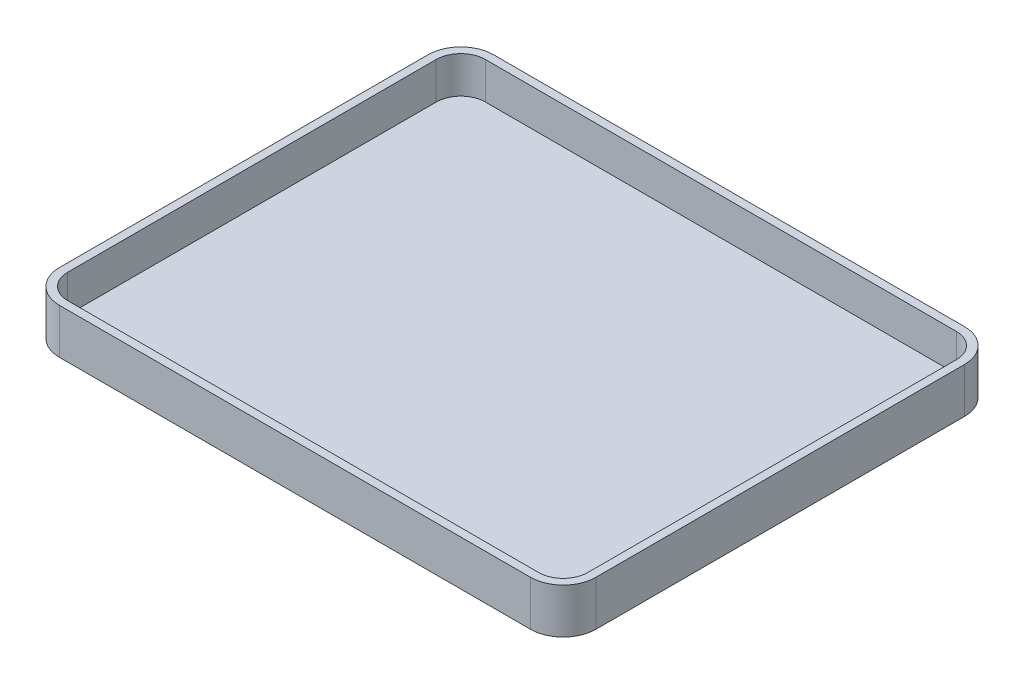
SolidWorks part; units mm, degrees
ref_plane "Alzado" through (0, 0, 0) normal (0, 0, 1) x (1, 0, 0)
ref_plane "Planta" through (0, 0, 0) normal (0, 1, 0) x (1, 0, 0)
ref_plane "Vista lateral" through (0, 0, 0) normal (1, 0, 0) x (0, 0, -1)
sketch "Croquis1" plane through (0, 0, 0) normal (0, 1, 0) x (1, 0, 0)
  line L0 (-65.5, 53) -> (-65.5, -53)
  line L1 (-63.5, 51) -> (63.5, 51)
  line L2 (-63.5, 51) -> (-63.5, -51)
  line L3 (-63.5, -51) -> (63.5, -51)
  line L4 (63.5, 51) -> (63.5, -51)
  line L5 (-63.5, 51) -> (63.5, -51) construction
  line L6 (-63.5, -51) -> (63.5, 51) construction
  line L7 (-65.5, -53) -> (65.5, -53)
  line L8 (65.5, 53) -> (65.5, -53)
  line L9 (-65.5, 53) -> (65.5, 53)
  line L10 (-60.3314, 19.4071) -> (299.002, 19.4071) construction
  line L11 (-45.0261, 11.6734) -> (-40.4305, 12.8223)
  line L12 (-39.5114, 12.8223) -> (-44.3368, 10.065)
  line L13 (-17.4526, 6.8481) -> (-13.5464, 6.6183)
  line L14 (-13.5464, 6.6183) -> (-10.5592, -1.8835)
  line L15 (-10.5592, -1.8835) -> (-7.5721, 6.6183)
  line L16 (-3.6659, 6.6183) -> (-3.8956, -6.0196)
  line L17 (-3.8956, -6.0196) -> (-5.9636, -5.7898)
  line L18 (-5.9636, -5.7898) -> (-6.1934, 2.9418)
  line L19 (-6.1934, 2.9418) -> (-9.6401, -6.0196)
  line L20 (-9.6401, -6.0196) -> (-11.7081, -5.7898)
  line L21 (-11.7081, -5.7898) -> (-14.925, 2.9418)
  line L22 (-14.925, 2.9418) -> (-15.3846, -6.0196)
  line L23 (-15.3846, -6.0196) -> (-17.4526, -5.7898)
  line L24 (-17.4526, -5.7898) -> (-17.4526, 6.8481)
  line L25 (7.5933, -2.1133) -> (1.1595, -2.3431)
  line L26 (5.5253, -3.2622) -> (7.5933, -3.492)
  line L27 (4.3764, 1.3334) -> (5.0658, -0.0453)
  line L28 (5.0658, -0.0453) -> (1.1595, -0.0453)
  line L29 (16.3249, 7.0778) -> (18.8525, 6.8481)
  line L30 (18.8525, 6.8481) -> (18.6227, -6.2493)
  line L31 (18.6227, -6.2493) -> (16.3249, -6.0196)
  line L32 (16.0952, 2.4823) -> (16.3249, 7.0778)
  line L33 (20.0014, 3.4014) -> (22.7588, 3.1716)
  line L34 (22.7588, 3.1716) -> (24.3672, -2.5729)
  line L35 (24.3672, -2.5729) -> (26.2054, 3.4014)
  line L36 (26.2054, 3.4014) -> (28.733, 3.1716)
  line L37 (28.733, 3.1716) -> (30.3415, -2.8027)
  line L38 (30.3415, -2.8027) -> (32.1797, 3.4014)
  line L39 (32.1797, 3.4014) -> (34.7073, 3.1716)
  line L40 (34.7073, 3.1716) -> (31.7201, -6.2493)
  line L41 (31.7201, -6.2493) -> (28.9628, -6.0196)
  line L42 (28.9628, -6.0196) -> (27.3543, -0.2751)
  line L43 (27.3543, -0.2751) -> (25.7459, -6.2493)
  line L44 (25.7459, -6.2493) -> (22.7588, -6.0196)
  line L45 (22.7588, -6.0196) -> (20.0014, 3.4014)
  line L46 (38.3837, 0.4142) -> (35.8562, 0.644)
  line L47 (41.6006, -1.6538) -> (41.8304, -2.8027)
  line L48 (38.6135, -4.4111) -> (38.154, -3.492)
  line L49 (45.5069, 3.4014) -> (48.494, 3.1716)
  line L50 (48.494, 3.1716) -> (50.3322, -2.8027)
  line L51 (50.3322, -2.8027) -> (52.4003, 3.4014)
  line L52 (52.4003, 3.4014) -> (55.1576, 3.1716)
  line L53 (46.1962, -9.4663) -> (46.426, -7.1685)
  line L54 (46.426, -7.1685) -> (47.8047, -7.3982)
  ellipse E0 centre (14.0074, -1.4088) end of major axis (14.1398, -4.5131) minor radius 2.2912
  spline S0 degree 3 poles (-44.3368, 10.065) (-44.4134, 9.8352) (-44.3953, 9.5469) (-44.5665, 9.3756) (-44.8087, 9.1334) (-45.2601, 9.1739) (-45.4857, 8.9161) (-45.824, 8.5294) (-45.8763, 7.9555) (-46.175, 7.5374) (-46.2745, 7.398) (-46.5276, 7.4414) (-46.6345, 7.3076) (-46.8485, 7.0401) (-46.9041, 6.6735) (-47.0941, 6.3885) (-47.2143, 6.2083) (-47.4568, 6.1227) (-47.5537, 5.9289) (-47.6949, 5.6465) (-47.6662, 5.303) (-47.7834, 5.0098) (-47.8237, 4.9093) (-47.9743, 4.8811) (-48.0132, 4.7801) (-48.361, 3.8758) (-48.7538, 2.9749) (-48.9323, 2.0227) (-49.2161, 0.5096) (-49.2387, -1.041) (-49.3919, -2.5729) knots 0 0 0 0 1 1 1 2 2 2 3 3 3 4 4 4 5 5 5 6 6 6 7 7 7 8 8 8 9 9 9 10 10 10 10
  spline S1 degree 3 poles (-49.3919, -3.0324) (-50.4276, -2.5146) (-50.8616, -2.0701) (-51.2301, -0.9644) knots 0 0 0 0 1 1 1 1
  spline S2 degree 3 poles (-51.9195, -0.7346) (-52.0727, 0.1845) (-52.4564, 1.0941) (-52.379, 2.0227) (-52.2337, 3.7666) (-51.3282, 5.4241) (-50.311, 6.8481) (-49.9962, 7.2888) (-49.4946, 7.5694) (-49.1621, 7.997) (-48.9518, 8.2673) (-48.9448, 8.6739) (-48.7026, 8.9161) (-48.5313, 9.0873) (-48.2103, 9.0051) (-48.0132, 9.1459) (-47.8677, 9.2498) (-46.7756, 10.5954) (-46.4048, 10.7543) (-46.0458, 10.9082) (-45.6388, 10.9075) (-45.2559, 10.9841) knots 0 0 0 0 1 1 1 2 2 2 3 3 3 4 4 4 5 5 5 6 6 6 7 7 7 7
  spline S3 degree 3 poles (-31.0096, -6.7089) (-31.3306, -7.1583) (-31.5555, -7.6804) (-31.9287, -8.0876) (-32.6643, -8.89) (-33.5505, -9.5518) (-34.4563, -10.1556) (-35.0575, -10.5564) (-35.6407, -10.9968) (-36.2945, -11.3045) (-36.952, -11.6139) (-37.6638, -11.7942) (-38.3625, -11.9938) (-39.2735, -12.2541) (-40.1743, -12.6241) (-41.1198, -12.6832) (-43.7095, -12.845) (-44.9482, -12.7603) (-46.8643, -11.9938) (-46.9649, -11.9536) (-46.9935, -11.8043) (-47.0941, -11.764) (-47.3873, -11.6468) (-47.72, -11.6516) (-48.0132, -11.5343) (-48.2144, -11.4538) (-48.3196, -11.2279) (-48.4728, -11.0747) (-49.123, -10.4245) (-49.8231, -9.7996) (-50.311, -9.0067) (-50.6701, -8.4233) (-50.9805, -7.8064) (-51.2301, -7.1685) (-52.4275, -4.1086) (-52.379, -4.8655) (-52.379, -3.2622) knots 13 13 13 13 14 14 14 15 15 15 16 16 16 17 17 17 18 18 18 19 19 19 20 20 20 21 21 21 22 22 22 23 23 23 24 24 24 25 25 25 25
  spline S4 degree 3 poles (-52.379, -3.2622) (-52.0727, -3.3388) (-51.7102, -3.2995) (-51.4599, -3.492) (-50.6872, -4.0864) (-50.1361, -4.9303) (-49.3919, -5.56) (-49.1304, -5.7813) (-48.7515, -5.8205) (-48.4728, -6.0196) (-48.2084, -6.2084) (-48.0741, -6.5636) (-47.7834, -6.7089) (-47.2847, -6.9583) (-46.6971, -6.9727) (-46.175, -7.1685) (-46.0736, -7.2065) (-46.0458, -7.358) (-45.9452, -7.3982) (-45.2706, -7.6681) (-44.5897, -7.9451) (-43.8772, -8.0876) (-42.6662, -8.3298) (-41.435, -8.5046) (-40.2007, -8.5471) (-38.2981, -8.6127) (-35.8994, -8.005) (-34.2265, -7.1685) (-33.7047, -6.9076) (-33.1398, -6.74) (-32.618, -6.4791) (-31.9717, -6.156) (-31.4653, -5.5587) (-30.7798, -5.3302) (-30.6173, -5.2761) (-30.3202, -5.3887) (-30.3202, -5.56) (-30.3202, -6.4618) (-30.6982, -6.273) (-31.0096, -6.7089) knots 0 0 0 0 1 1 1 2 2 2 3 3 3 4 4 4 5 5 5 6 6 6 7 7 7 8 8 8 9 9 9 10 10 10 11 11 11 12 12 12 13 13 13 13
  spline S5 degree 3 poles (-31.4691, -14.0618) (-34.1314, -15.2906) (-37.3071, -15.9228) (-40.2007, -15.4405) (-40.3076, -15.4227) (-40.3239, -15.2301) (-40.4305, -15.2107) (-41.1878, -15.073) (-41.9981, -15.2244) (-42.7283, -14.981) (-42.8908, -14.9268) (-42.6559, -14.5889) (-42.4985, -14.5214) (-42.0703, -14.3379) (-41.58, -14.3643) (-41.1198, -14.2916) (-40.1248, -14.1345) (-39.1178, -14.0431) (-38.1327, -13.8321) (-38.0268, -13.8094) (-38.0035, -13.6425) (-37.9029, -13.6023) (-37.2283, -13.3324) (-36.5096, -13.1828) (-35.8349, -12.9129) (-35.2275, -12.67) (-34.5809, -12.1146) (-33.9967, -11.764) (-32.5277, -10.8827) (-31.8287, -10.3179) (-30.7798, -9.0067) (-30.5091, -8.6684) (-30.0836, -8.4591) (-29.8607, -8.0876) (-29.5606, -7.5874) (-29.4322, -7.0009) (-29.1713, -6.4791) (-28.4572, -5.0508) (-27.8289, -3.9389) (-27.5629, -2.3431) (-27.4097, -1.424) (-27.1033, -0.5175) (-27.1033, 0.4142) (-27.1033, 2.7445) (-27.4377, 4.2444) (-28.0224, 6.3885) (-28.0509, 6.493) (-28.2038, 6.5214) (-28.2522, 6.6183) (-28.6661, 7.4461) (-28.9623, 8.331) (-29.4011, 9.1459) (-29.5038, 9.3366) (-29.7405, 9.4252) (-29.8607, 9.6054) (-30.0507, 9.8904) (-30.2531, 10.1886) (-30.3202, 10.5245) (-30.3415, 10.6307) (-30.167, 10.6777) (-30.0905, 10.7543) knots 20 20 20 20 21 21 21 22 22 22 23 23 23 24 24 24 25 25 25 26 26 26 27 27 27 28 28 28 29 29 29 30 30 30 31 31 31 32 32 32 33 33 33 34 34 34 35 35 35 36 36 36 37 37 37 38 38 38 39 39 39 40 40 40 40
  spline S6 degree 3 poles (-30.0905, 10.7543) (-29.1914, 10.4546) (-28.9328, 10.1923) (-28.2522, 9.3756) (-28.1426, 9.2441) (-28.1595, 9.0188) (-28.0224, 8.9161) (-27.8287, 8.7707) (-27.5044, 8.8576) (-27.3331, 8.6863) (-26.4894, 7.8426) (-26.1071, 6.6787) (-25.4949, 5.6992) (-25.3801, 5.5155) (-25.1158, 5.4408) (-25.0353, 5.2396) (-24.8007, 4.6532) (-24.7755, 4.0006) (-24.5758, 3.4014) (-24.5415, 3.2986) (-24.3722, 3.2767) (-24.346, 3.1716) (-24.0618, 2.0349) (-23.6892, 0.8961) (-23.6566, -0.2751) (-23.6118, -1.8902) (-23.8979, -3.4995) (-24.1162, -5.1005) (-24.1308, -5.2078) (-24.3117, -5.2275) (-24.346, -5.3302) (-24.5457, -5.9294) (-24.571, -6.582) (-24.8055, -7.1685) (-24.886, -7.3696) (-25.1536, -7.4423) (-25.2651, -7.628) (-25.4413, -7.9217) (-25.5282, -8.2665) (-25.7246, -8.5471) (-26.1997, -9.2259) (-26.5787, -9.9739) (-27.1033, -10.6152) (-27.2782, -10.8289) (-27.6201, -10.8591) (-27.7927, -11.0747) (-27.944, -11.2638) (-27.8512, -11.5928) (-28.0224, -11.764) (-28.2646, -12.0063) (-28.6628, -12.0245) (-28.9416, -12.2236) (-29.206, -12.4125) (-29.3665, -12.7241) (-29.6309, -12.9129) (-29.9096, -13.112) (-30.2595, -13.191) (-30.55, -13.3725) (-30.8748, -13.5755) (-31.1214, -13.9014) (-31.4691, -14.0618) knots 0 0 0 0 1 1 1 2 2 2 3 3 3 4 4 4 5 5 5 6 6 6 7 7 7 8 8 8 9 9 9 10 10 10 11 11 11 12 12 12 13 13 13 14 14 14 15 15 15 16 16 16 17 17 17 18 18 18 19 19 19 20 20 20 20
  spline S7 degree 3 poles (-7.5721, 6.6183) (-7.1125, 6.6949) (-6.6593, 6.8481) (-6.1934, 6.8481) (-5.3474, 6.8481) (-4.5084, 6.6949) (-3.6659, 6.6183) knots 0 0 0 0 1 1 1 2 2 2 2
  spline S8 degree 3 poles (7.5933, -3.492) (7.3373, -4.5162) (7.5869, -4.1878) (7.1338, -4.6409) (6.7508, -5.0239) (6.4551, -5.5211) (5.9849, -5.7898) (5.354, -6.1503) (4.6402, -6.4102) (3.9169, -6.4791) (2.772, -6.5882) (1.0085, -6.4331) (0.0106, -5.56) (-1.7342, -4.0333) (-1.7519, -1.9723) (-1.5978, 0.1845) (-1.5901, 0.2925) (-1.4165, 0.3174) (-1.3681, 0.4142) (-1.1072, 0.936) (-1.0218, 1.551) (-0.6787, 2.0227) (-0.3903, 2.4193) (0.0564, 2.6785) (0.4702, 2.9418) (0.9036, 3.2177) (1.3374, 3.5824) (1.8488, 3.6312) (2.9951, 3.7403) (4.153, 3.5442) (5.2955, 3.4014) (5.403, 3.3879) (5.4407, 3.2393) (5.5253, 3.1716) (6.1856, 2.6433) (7.0143, 2.1715) (7.3635, 1.3334) (7.6065, 0.7503) (7.7811, 0.1253) (7.8231, -0.5049) (7.8591, -1.0453) (7.6699, -1.5772) (7.5933, -2.1133) knots 0 0 0 0 1 1 1 2 2 2 3 3 3 4 4 4 5 5 5 6 6 6 7 7 7 8 8 8 9 9 9 10 10 10 11 11 11 12 12 12 13 13 13 14 14 14 14
  spline S9 degree 3 poles (1.1595, -2.3431) (1.2459, -2.7752) (1.2618, -3.7) (1.8488, -3.9516) (3.6525, -4.7246) (4.1926, -4.595) (5.5253, -3.2622) knots 0 0 0 0 1 1 1 2 2 2 2
  spline S10 degree 3 poles (1.1595, -0.0453) (1.3494, 0.4294) (1.5251, 1.4979) (2.3084, 1.5631) (2.9996, 1.6207) (3.6871, 1.41) (4.3764, 1.3334) knots 0 0 0 0 1 1 1 2 2 2 2
  spline S11 degree 3 poles (16.0952, -5.3302) (15.3292, -6.0962) (14.4647, -6.4791) (13.3378, -6.4791) (12.7203, -6.4791) (12.1024, -6.3833) (11.4996, -6.2493) (11.3938, -6.2259) (11.3464, -6.0962) (11.2698, -6.0196) (10.503, -5.2527) (9.7316, -4.7721) (9.4316, -3.7218) (8.9637, -2.0844) (8.6633, -0.6627) (9.4316, 0.8738) (9.616, 1.2427) (9.6335, 1.7006) (9.8911, 2.0227) (10.4795, 2.7581) (11.6436, 3.5684) (12.6485, 3.6312) (14.8723, 3.7701) (14.7322, 3.5045) (16.0952, 2.4823) knots 0 0 0 0 1 1 1 2 2 2 3 3 3 4 4 4 5 5 5 6 6 6 7 7 7 8 8 8 8
  spline S12 degree 3 poles (35.8562, 0.644) (36.0152, 1.5981) (35.9443, 2.1927) (36.7753, 2.712) (37.211, 2.9844) (37.7078, 3.1465) (38.154, 3.4014) (38.248, 3.4551) (38.2754, 3.6312) (38.3837, 3.6312) (42.8523, 3.6312) (41.9114, 4.4693) (43.2091, 3.1716) (43.5921, 2.7886) (44.2668, 2.5566) (44.358, 2.0227) (44.8228, -0.6995) (44.6644, -3.492) (44.8175, -6.2493) knots 0 0 0 0 1 1 1 2 2 2 3 3 3 4 4 4 5 5 5 6 6 6 6
  spline S13 degree 3 poles (44.8175, -6.2493) (41.8443, -6.0016) (42.7124, -6.6717) (41.6006, -5.56) knots 0 0 0 0 1 1 1 1
  spline S14 degree 3 poles (41.6006, -5.56) (41.4475, -5.7132) (41.3422, -5.9391) (41.1411, -6.0196) (40.5547, -6.2541) (39.9336, -6.4459) (39.3028, -6.4791) (38.4301, -6.5251) (36.3607, -6.5916) (35.8562, -5.3302) (35.354, -4.0748) (34.9988, -2.3019) (36.3157, -1.424) (36.6007, -1.234) (36.9025, -1.0475) (37.2348, -0.9644) (38.6776, -0.6037) (40.1707, -0.4539) (41.6006, -0.0453) knots 0 0 0 0 1 1 1 2 2 2 3 3 3 4 4 4 5 5 5 6 6 6 6
  spline S15 degree 3 poles (41.8304, 0.8738) (41.6006, 1.1036) (41.4453, 1.449) (41.1411, 1.5631) (39.5526, 2.1588) (39.0423, 1.7313) (38.3837, 0.4142) knots 0 0 0 0 1 1 1 2 2 2 2
  spline S16 degree 3 poles (41.8304, -2.8027) (41.5388, -3.0943) (41.6625, -3.6599) (41.3709, -3.9516) (40.3449, -4.9775) (39.8013, -4.6091) (38.6135, -4.4111) knots 0 0 0 0 1 1 1 2 2 2 2
  spline S17 degree 3 poles (38.154, -3.492) (38.3071, -3.1856) (38.3395, -2.7784) (38.6135, -2.5729) (39.4469, -1.9478) (40.5989, -1.94) (41.6006, -1.6538) knots 0 0 0 0 1 1 1 2 2 2 2
  spline S18 degree 3 poles (55.1576, 3.1716) (54.834, 1.8773) (54.475, 0.7385) (54.0087, -0.5049) (53.9707, -0.6063) (53.817, -0.6332) (53.7789, -0.7346) (53.5831, -1.2568) (53.5152, -1.821) (53.3194, -2.3431) (53.2813, -2.4445) (53.1276, -2.4715) (53.0896, -2.5729) (52.5965, -3.8879) (52.4338, -4.7046) (51.9407, -6.0196) (51.9027, -6.121) (51.749, -6.1479) (51.7109, -6.2493) (50.9769, -8.2066) (51.6932, -7.416) (51.0216, -8.0876) (50.6386, -8.4705) (50.3495, -8.9797) (49.8727, -9.2365) (48.4951, -9.9783) (47.6251, -9.6449) (46.1962, -9.4663) knots 0 0 0 0 1 1 1 2 2 2 3 3 3 4 4 4 5 5 5 6 6 6 7 7 7 8 8 8 9 9 9 9
  spline S19 degree 3 poles (48.494, -6.9387) (48.5706, -6.4791) (48.8198, -6.0159) (48.7238, -5.56) (48.504, -4.5161) (47.9532, -3.5704) (47.5749, -2.5729) (47.1107, -1.3491) (46.6395, -0.1279) (46.1962, 1.1036) (45.4827, 3.0857) (45.5069, 2.4617) (45.5069, 3.4014) knots 0 0 0 0 1 1 1 2 2 2 3 3 3 4 4 4 4
  point P0 (0, 0)
  dimension "D1" = 127
  dimension "D2" = 102
  dimension "D3" = 2
extrude "Saliente-Extruir2" add sketch "Croquis1" along normal blind 11
fillet "Redondeo1" radius 8 4 edges at (-65.5, 5.5, -53) (65.5, 5.5, -53) (65.5, 5.5, 53) (-65.5, 5.5, 53)
shell "Vaciado1" thickness 2
sketch "Croquis3" plane through (0, 0, 0) normal (0, -1, 0) x (1, 0, 0)
  line L0 (35.7047, 72.3651) -> (395.038, 72.3651) construction
  line L1 (-43.7957, -0.602) -> (-44.7734, -0.211)
  line L2 (-44.7734, -0.211) -> (-45.6758, 0.9833)
  line L3 (-16.3093, 8.1491) -> (-12.7264, 7.95)
  line L4 (-12.7264, 7.95) -> (-10.1388, 0.7843)
  line L5 (-10.1388, 0.7843) -> (-7.5512, 8.1491)
  line L6 (-7.5512, 8.1491) -> (-3.9683, 7.95)
  line L7 (-3.9683, 7.95) -> (-4.1673, -3.3958)
  line L8 (-4.1673, -3.3958) -> (-6.3569, -3.1967)
  line L9 (-6.3569, -3.1967) -> (-6.5559, 4.1681)
  line L10 (-6.5559, 4.1681) -> (-9.1436, -3.3958)
  line L11 (-9.1436, -3.3958) -> (-11.3331, -3.1967)
  line L12 (-11.3331, -3.1967) -> (-13.9207, 4.3672)
  line L13 (-13.9207, 4.3672) -> (-14.1198, -3.3958)
  line L14 (-14.1198, -3.3958) -> (-16.5084, -3.1967)
  line L15 (-16.5084, -3.1967) -> (-16.3093, 8.1491)
  line L16 (5.9842, 0.3862) -> (0.0127, -0.0119)
  line L17 (3.7946, -0.8081) -> (5.5861, -1.0072)
  line L18 (2.7994, 3.1729) -> (3.3965, 1.9786)
  line L19 (3.3965, 1.9786) -> (0.0127, 1.9786)
  line L20 (12.9509, 8.1491) -> (15.3395, 7.95)
  line L21 (15.3395, 7.95) -> (15.1404, -3.3958)
  line L22 (15.1404, -3.3958) -> (13.15, -3.1967)
  line L23 (12.9509, 4.1681) -> (12.9509, 8.1491)
  line L24 (16.3347, 4.9643) -> (18.7233, 4.7653)
  line L25 (18.7233, 4.7653) -> (20.1167, -0.211)
  line L26 (20.1167, -0.211) -> (21.51, 4.9643)
  line L27 (21.51, 4.9643) -> (23.8986, 4.7653)
  line L28 (23.8986, 4.7653) -> (25.292, -0.211)
  line L29 (25.292, -0.211) -> (26.6853, 4.9643)
  line L30 (26.6853, 4.9643) -> (29.0739, 4.7653)
  line L31 (29.0739, 4.7653) -> (26.4862, -3.3958)
  line L32 (26.4862, -3.3958) -> (23.8986, -3.1967)
  line L33 (23.8986, -3.1967) -> (22.7043, 1.5805)
  line L34 (22.7043, 1.5805) -> (21.311, -3.3958)
  line L35 (21.311, -3.3958) -> (18.7233, -3.1967)
  line L36 (18.7233, -3.1967) -> (16.3347, 4.9643)
  line L37 (32.0596, 2.3767) -> (30.0894, 2.3767)
  line L38 (35.4435, 0.5213) -> (35.2363, -1.0692)
  line L39 (38.4292, 4.9643) -> (41.0168, 4.7653)
  line L40 (41.0168, 4.7653) -> (42.6092, -0.41)
  line L41 (42.6092, -0.41) -> (44.4007, 4.9643)
  line L42 (44.4007, 4.9643) -> (46.7893, 4.7653)
  line L43 (39.0263, -5.9834) -> (39.2254, -4.192)
  line L44 (39.2254, -4.192) -> (40.6187, -4.391)
  line L45 (41.2159, -3.7939) -> (38.4292, 4.9643)
  line L49 (32.3732, 2.62) -> (32.2587, 2.3767)
  arc A0 (3.7946, -0.8081) -> (0.0127, -0.0119) centre (2.0311, 0.1953) cw
  ellipse E0 centre (11.1194, 0.8206) end of major axis (11.1554, -1.8699) minor radius 1.9649
  spline S0 degree 3 poles (-29.8447, -3.9929) (-29.2525, -3.7776) (-27.257, -1.7538) (-27.257, -2.5996) (-27.257, -4.1524) (-29.907, -6.3419) (-31.039, -6.9786) (-35.2673, -9.3571) (-42.0186, -10.4827) (-44.7734, -5.5853) (-45.5687, -4.1713) (-46.3658, -2.2563) (-46.3658, -0.6091) knots 4 4 4 4 5 5 5 6 6 6 7 7 7 8 8 8 8
  spline S1 degree 3 poles (-46.3658, -0.6091) (-46.1667, -0.6754) (-45.9325, -0.677) (-45.7686, -0.8081) (-45.2557, -1.2184) (-44.8595, -1.7576) (-44.3753, -2.2015) (-42.0352, -4.3465) (-38.3261, -5.4776) (-35.219, -5.3862) (-33.6909, -5.3413) (-31.3622, -4.5447) (-29.8447, -3.9929) knots 0 0 0 0 1 1 1 2 2 2 3 3 3 4 4 4 4
  spline S2 degree 3 poles (-46.0388, 1.4423) (-46.1668, 2.2392) (-46.4946, 3.0292) (-46.4228, 3.8332) (-46.0277, 8.2602) (-39.6389, 13.7804) (-35.2213, 13.1228) knots 0 0 0 0 1 1 1 2 2 2 2
  spline S3 degree 3 poles (-35.2213, 13.1228) (-35.2877, 13.0565) (-35.3366, 12.9659) (-35.4206, 12.924) (-36.1381, 12.5663) (-36.9049, 12.3105) (-37.6112, 11.9312) (-37.9334, 11.7582) (-38.0953, 11.3233) (-38.4083, 11.1359) (-42.559, 8.6518) (-43.4422, 3.9278) (-43.7957, -0.602) knots 0 0 0 0 1 1 1 2 2 2 3 3 3 4 4 4 4
  spline S4 degree 3 poles (-38.2047, -10.3625) (-37.1573, -10.1776) (-36.0763, -10.2877) (-35.02, -10.1634) (-32.3645, -9.851) (-29.1646, -7.3388) (-27.4561, -5.3862) (-26.1886, -3.9377) (-25.0838, -1.6974) (-24.8684, 0.1871) (-24.4914, 3.4864) (-24.5793, 6.5392) (-26.2618, 9.3434) (-26.7734, 10.1961) (-27.5354, 10.9746) (-27.8542, 11.931) knots 5 5 5 5 6 6 6 7 7 7 8 8 8 9 9 9 10 10 10 10
  spline S5 degree 3 poles (-27.8542, 11.931) (-26.5314, 11.6003) (-25.6259, 10.4989) (-24.6694, 9.5424) (-19.5177, 4.3908) (-20.644, -5.5426) (-26.8589, -9.3672) (-27.6493, -9.8536) (-29.4752, -11.0061) (-30.4418, -11.1587) (-32.4343, -11.4733) (-36.4536, -12.0607) (-38.4038, -10.7606) (-38.5272, -10.6783) (-38.3508, -10.3883) (-38.2047, -10.3625) knots 0 0 0 0 1 1 1 2 2 2 3 3 3 4 4 4 5 5 5 5
  spline S6 degree 3 poles (5.5861, -1.0072) (5.275, -2.2513) (4.2043, -3.461) (2.7994, -3.5948) (-1.2746, -3.9828) (-2.6537, -1.7113) (-2.3759, 2.1776) (-2.3692, 2.2712) (-2.2188, 2.2927) (-2.1768, 2.3767) (-1.6092, 3.5119) (-0.9504, 5.0148) (0.6099, 5.1634) (1.6028, 5.2579) (2.6058, 5.088) (3.5956, 4.9643) (3.6887, 4.9527) (3.7226, 4.8253) (3.7946, 4.7653) (5.3868, 3.4384) (5.6422, 2.4379) (5.9842, 0.3862) knots 0 0 0 0 1 1 1 2 2 2 3 3 3 4 4 4 5 5 5 6 6 6 7 7 7 7
  spline S7 degree 3 poles (0.0127, 1.9786) (0.6605, 3.598) (1.0655, 3.3896) (2.7994, 3.1729) knots 0 0 0 0 1 1 1 1
  spline S8 degree 3 poles (12.9509, -2.5996) (12.343, -3.2075) (12.1946, -3.5339) (11.1595, -3.5948) (5.3557, -3.9362) (6.0058, 4.2669) (8.9699, 4.9643) (10.8681, 5.4109) (11.7477, 5.3713) (12.9509, 4.1681) knots 0 0 0 0 1 1 1 2 2 2 3 3 3 3
  spline S9 degree 3 poles (30.0894, 2.3767) (30.2361, 3.1421) (30.2019, 3.756) (30.9289, 4.1482) (31.3206, 4.3596) (31.7456, 4.5048) (32.1373, 4.7162) (32.2199, 4.7607) (32.2473, 4.9126) (32.3411, 4.9103) (36.211, 4.8162) (35.4138, 5.5619) (36.5103, 4.4107) (36.8339, 4.071) (37.4114, 3.8555) (37.481, 3.3916) (37.8262, 1.0913) (37.6334, -1.258) (37.7097, -3.5828) knots 0 0 0 0 1 1 1 2 2 2 3 3 3 4 4 4 5 5 5 6 6 6 6
  spline S10 degree 3 poles (37.7097, -3.5828) (36.6453, -3.6659) (35.715, -3.8333) (34.9682, -2.9434) knots 0 0 0 0 1 1 1 1
  spline S11 degree 3 poles (34.9682, -2.9434) (34.8275, -3.0676) (34.7274, -3.2678) (34.5461, -3.3159) (33.892, -3.4894) (33.2112, -3.5956) (32.5346, -3.5889) (31.9338, -3.583) (31.2786, -3.5802) (30.7591, -3.2784) (29.5348, -2.5675) (29.8078, -1.3502) (29.7535, -0.224) knots 0 0 0 0 1 1 1 2 2 2 3 3 3 4 4 4 4
  spline S12 degree 3 poles (29.7535, -0.224) (30.0194, 0.0099) (30.0672, 0.4471) (30.3573, 0.6502) (30.8023, 0.9618) (31.3264, 1.1752) (31.8586, 1.2843) (33.8778, 1.6983) (34.4089, 0.8263) (35.0314, 2.359) knots 0 0 0 0 1 1 1 2 2 2 3 3 3 3
  spline S13 degree 1 poles (34.8323, 2.9561) (35.0314, 2.359) knots 0 0 1 1
  spline S14 degree 3 poles (35.2363, -1.0692) (34.9949, -1.2502) (34.9754, -1.6515) (34.7208, -1.8134) (33.5761, -2.5414) (33.3803, -2.226) (32.2587, -1.8699) knots 0 0 0 0 1 1 1 2 2 2 2
  spline S15 degree 3 poles (31.9806, -0.8081) (32.1608, -0.5373) (32.2389, -0.1574) (32.5211, 0.0043) (33.3796, 0.4959) (34.4661, 0.3686) (35.4435, 0.5213) knots 0 0 0 0 1 1 1 2 2 2 2
  spline S16 degree 3 poles (46.7893, 4.7653) (46.6144, 3.8907) (46.3102, 3.0233) (45.9931, 2.1776) (45.9601, 2.0898) (45.8261, 2.0668) (45.794, 1.9786) (45.5573, 1.3276) (45.4336, 0.6391) (45.1969, -0.0119) (45.1648, -0.1001) (45.0308, -0.1231) (44.9978, -0.211) (44.6295, -1.1933) (44.3709, -2.2144) (44.0026, -3.1967) (43.9696, -3.2846) (43.8365, -3.3079) (43.8035, -3.3958) (43.1677, -5.0913) (43.7882, -4.4064) (43.2064, -4.9881) (42.8746, -5.3199) (42.6363, -5.785) (42.2111, -5.9834) (40.6098, -6.7307) (40.366, -6.4299) (39.0263, -5.9834) knots 0 0 0 0 1 1 1 2 2 2 3 3 3 4 4 4 5 5 5 6 6 6 7 7 7 8 8 8 9 9 9 9
  spline S17 degree 1 poles (32.0596, 2.3767) (32.2587, 2.3767) knots 0 0 1 1
  spline S18 degree 2 poles (32.2587, -1.8699) (31.6759, -1.4996) (31.9806, -0.8081) knots 0 0 0 1 1 1
  spline S20 degree 1 poles (-46.0388, 1.4423) (-45.6758, 0.9833) knots 0 0 1 1
  spline S21 degree 3 poles (34.8323, 2.9561) (34.642, 3.0329) (34.4623, 3.2281) (34.2613, 3.1864) (33.6179, 3.0528) (33.0025, 2.8088) (32.3732, 2.62) knots 0 0 0 0 1 1 1 2 2 2 2
  spline S22 degree 2 poles (13.15, -3.1967) (13.5027, -2.4782) (12.9509, -2.5996) knots 0 0 0 1 1 1
  spline S23 degree 2 poles (41.2159, -3.7939) (41.4885, -4.6807) (40.6187, -4.391) knots 0 0 0 1 1 1
extrude "Cortar-Extruir1" cut sketch "Croquis3" against normal blind 1
